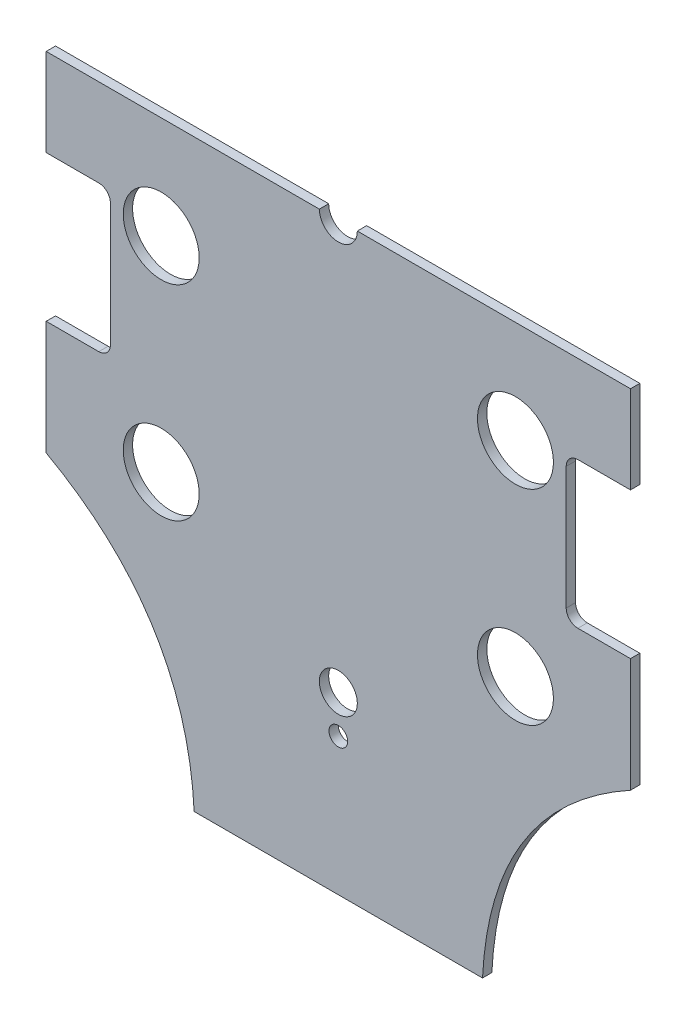
SolidWorks part; units mm, degrees
ref_plane "前视基准面" through (0, 0, 0) normal (0, 0, 1) x (1, 0, 0)
ref_plane "上视基准面" through (0, 0, 0) normal (0, 1, 0) x (1, 0, 0)
ref_plane "右视基准面" through (0, 0, 0) normal (1, 0, 0) x (0, 0, -1)
sketch "草图1" plane through (0, 0, 0) normal (0, 0, 1) x (1, 0, 0)
  line L0 (0, 35) -> (0, -65) construction
  line L1 (-50, 0) -> (50, 0) construction
  line L2 (-50, 20) -> (-41, 20)
  line L3 (-50, 35) -> (-3.25, 35)
  line L4 (-50, 35) -> (-50, 20)
  line L5 (-24.6738, -65) -> (24.6738, -65)
  line L6 (50, 35) -> (50, 20)
  line L7 (-39, 18) -> (-39, -3)
  line L8 (-41, -5) -> (-50, -5)
  line L12 (-50, -5) -> (-50, -24.5069)
  line L13 (39, 18) -> (39, -3)
  line L14 (50, 20) -> (41, 20)
  line L15 (41, -5) -> (50, -5)
  line L16 (50, -5) -> (50, -24.5069)
  line L17 (3.25, 35) -> (50, 35)
  circle A2 centre (0, -35) radius 3.25
  circle A3 centre (30.3109, -17.5) radius 6.5
  circle A4 centre (30.3109, 17.5) radius 6.5
  circle A5 centre (-30.3109, 17.5) radius 6.5
  circle A6 centre (-30.3109, -17.5) radius 6.5
  arc A7 (-3.25, 35) -> (3.25, 35) centre (0, 35) ccw
  circle A8 centre (0, -41.5) radius 1.6
  arc A9 (-39, -3) -> (-41, -5) centre (-41, -3) cw
  arc A10 (-41, 20) -> (-39, 18) centre (-41, 18) cw
  arc A11 (39, -3) -> (41, -5) centre (41, -3) ccw
  arc A12 (41, 20) -> (39, 18) centre (41, 18) ccw
  spline S0 degree 2 poles (-50, -24.5069) (-26.057, -37.7516) (-24.6738, -65) knots 0 0 0 1 1 1
  spline S1 degree 2 poles (50, -24.5069) (26.057, -37.7516) (24.6738, -65) knots 0 0 0 1 1 1
  dimension "D3" = 13
  dimension "D4" = 13
  dimension "D5" = 13
  dimension "D6" = 13
  dimension "D8" = 6.5
  dimension "D1" = 6.5
  dimension "D2" = 3.2
  dimension "D12" = 2
  dimension "D7" = 100
extrude "凸台-拉伸2" add sketch "草图1" along normal blind 1.6
